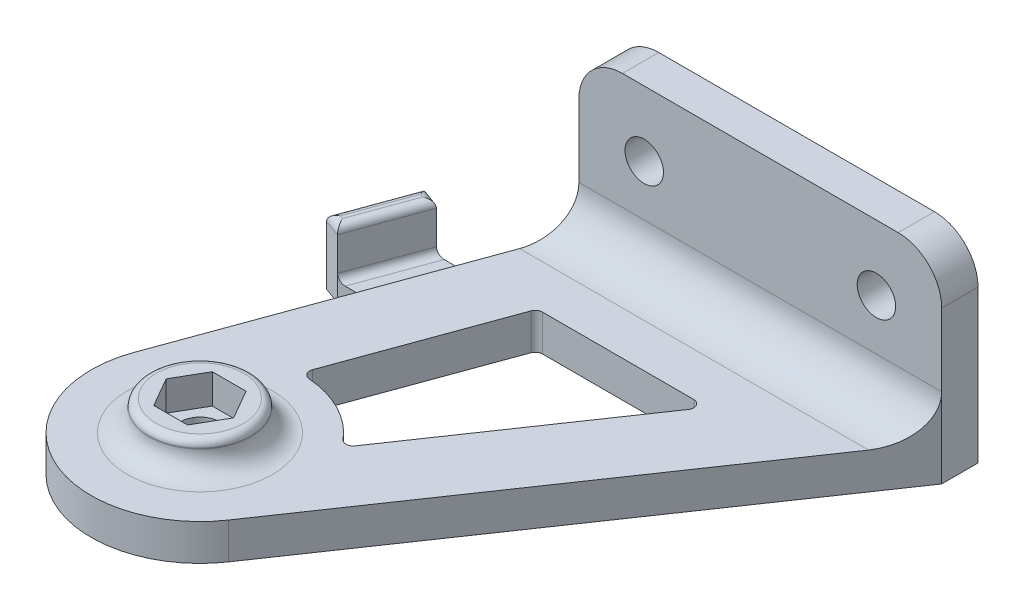
SolidWorks part; units mm, degrees
ref_plane "Front Plane" through (0, 0, 0) normal (0, 0, 1) x (1, 0, 0)
ref_plane "Top Plane" through (0, 0, 0) normal (0, 1, 0) x (1, 0, 0)
ref_plane "Right Plane" through (0, 0, 0) normal (1, 0, 0) x (0, 0, -1)
sketch "Sketch1" plane through (0, 0, 0) normal (0, 0, 1) x (1, 0, 0)
  line L1 (0, 0) -> (-300, 0)
  line L2 (0, 0) -> (0, -20)
  line L3 (0, -20) -> (-300, -20)
  line L4 (-300, 0) -> (-300, -20)
  line L5 (0, 0) -> (-18, 0)
  line L6 (0, 0) -> (0, -20)
  line L7 (0, -20) -> (-18, -20)
  line L8 (-18, 0) -> (-18, -20)
  dimension "D1" = 20
  dimension "D2" = 300
  dimension "D3" = 18
sketch "Sketch2" plane through (0, 0, 0) normal (1, 0, 0) x (0, 0, -1)
  line L1 (0, -20) -> (20, -20)
  line L2 (0, -20) -> (0, -320)
  line L3 (0, -320) -> (20, -320)
  line L4 (20, -20) -> (20, -320)
  line L5 (0, -20) -> (20, -20)
  line L6 (0, -20) -> (0, -38)
  line L7 (0, -38) -> (20, -38)
  line L8 (20, -20) -> (20, -38)
  dimension "D1" = 20
  dimension "D2" = 300
  dimension "D3" = 18
sketch "Sketch3" plane through (0, 0, 0) normal (0, 0, 1) x (1, 0, 0)
  line L1 (-88, -1) -> (-38, -1)
  line L2 (-88, -1) -> (-88, -28)
  line L3 (-88, -28) -> (-38, -28)
  line L4 (-38, -1) -> (-38, -28)
  line L5 (-18, 0) -> (-18, -20) construction
  line L6 (0, 0) -> (-300, 0) construction
  line L7 (0, -20) -> (-300, -20) construction
  dimension "D1" = 20
  dimension "D2" = 1
  dimension "D3" = 50
  dimension "D4" = 8
extrude "Boss-Extrude1" add sketch "Sketch3" along normal blind 5 contours L3 L4 L1 L2
sketch "Sketch5" plane through (0, -28, 0) normal (0, -1, 0) x (1, 0, 0)
  line L0 (-38, 5) -> (-77.8415, 63.4486)
  line L1 (-104.3312, 49.8697) -> (-88, 5)
  line L2 (-88, 5) -> (-88, 0)
  line L3 (-88, 0) -> (-38, 0)
  line L4 (-38, 0) -> (-38, 5)
  line L5 (-88, 5) -> (-88, 0) construction
  line L6 (-88, 5) -> (-38, 5) construction
  arc A0 (-77.8415, 63.4486) -> (-104.3312, 49.8697) centre (-90.2358, 55) ccw
  dimension "D2" = 15
  dimension "D1" = 160
  dimension "D3" = 50
extrude "Boss-Extrude2" add sketch "Sketch5" against normal blind 5
hole_wizard "M5 Clearance Hole1" positions "Sketch6" profile "Sketch7" hole size "M5" standard "ISO" end condition through all
sketch "Sketch6" plane through (0, 0, 5) normal (0, 0, 1) x (1, 0, 0)
  line L0 (-79, -10) -> (-47, -10) construction
  line L2 (-63, -10) -> (-63, -1) construction
  line L3 (-88, -1) -> (-38, -1) construction
  line L5 (0, 0) -> (-300, 0) construction
  point P0 (-79, -10)
  point P2 (-47, -10)
  dimension "D1" = 10
  dimension "D2" = 32
sketch "Sketch7" plane through (-79, -10, 5) normal (1, 0, 0) x (0, -1, 0)
  line L0 (0, 0) -> (0, 5)
  line L1 (0, 5) -> (2.65, 5)
  line L2 (2.65, 5) -> (2.65, 0)
  line L5 (2.65, 0) -> (0, 0)
  line L11 (0, -6.35) -> (0, 107.95) construction
  dimension "Thru Hole Dia." = 5.3
  dimension "Thru Hole Depth" = 5
fillet "Fillet1" radius 6 3 edges at (-88, -1, 2.5) (-38, -1, 2.5) (-63, -23, 5)
hole_wizard "M5 Clearance Hole2" positions "Sketch8" profile "Sketch9" hole size "M5" standard "ISO" end condition through all
sketch "Sketch8" plane through (0, -23, 0) normal (0, 1, 0) x (1, 0, 0)
  point P0 (-90.2358, -55)
sketch "Sketch9" plane through (-90.2358, -23, 55) normal (1, 0, 0) x (0, 0, 1)
  line L0 (0, 0) -> (0, 5)
  line L1 (0, 5) -> (2.65, 5)
  line L2 (2.65, 5) -> (2.65, 0)
  line L5 (2.65, 0) -> (0, 0)
  line L11 (0, -6.35) -> (0, 107.95) construction
  dimension "Thru Hole Dia." = 5.3
  dimension "Thru Hole Depth" = 5
sketch "Sketch10" plane through (0, -23, 0) normal (0, 1, 0) x (1, 0, 0)
  line L0 (-42.0899, -11) -> (-90.1838, -11) construction
  line L1 (-92.5626, -50.97) -> (-94.8893, -55)
  line L2 (-94.8893, -55) -> (-92.5626, -59.03)
  line L3 (-92.5626, -59.03) -> (-87.9091, -59.03)
  line L4 (-87.9091, -59.03) -> (-85.5824, -55)
  line L5 (-85.5824, -55) -> (-87.9091, -50.97)
  line L6 (-87.9091, -50.97) -> (-92.5626, -50.97)
  circle A0 centre (-90.2358, -55) radius 4.03 construction
  dimension "D1" = 8.06
sketch "Sketch11" plane through (0, -23, 0) normal (0, 1, 0) x (1, 0, 0)
  circle A0 centre (-90.2358, -55) radius 7
  dimension "D1" = 14
extrude "Boss-Extrude3" add sketch "Sketch11" along normal blind 4.1
extrude "Cut-Extrude1" cut sketch "Sketch10" along normal through all
fillet "Fillet2" radius 3 1 edges at (-90.2358, -23, 48)
fillet "Fillet3" radius 1 1 edges at (-90.2358, -18.9, 62)
sketch "Sketch12" plane through (0, 0, 0) normal (0, 0, -1) x (-1, 0, 0)
  line L0 (47, -10) -> (63, -10) construction
  line L1 (56, -12.25) -> (70, -12.25)
  line L2 (56, -12.25) -> (56, -7.75)
  line L3 (56, -7.75) -> (70, -7.75)
  line L4 (70, -12.25) -> (70, -7.75)
  line L5 (56, -12.25) -> (70, -7.75) construction
  line L6 (56, -7.75) -> (70, -12.25) construction
  line L7 (63, -10) -> (79, -10) construction
  circle A0 centre (79, -10) radius 2.65 construction
  point P0 (63, -10)
  dimension "D1" = 4.5
  dimension "D2" = 14
extrude "Boss-Extrude4" add sketch "Sketch12" along normal blind 2.5
sketch "Sketch13" plane through (0, -28, 0) normal (0, -1, 0) x (1, 0, 0)
  line L0 (-91.6397, 15) -> (-97.6397, 15)
  line L1 (-104.3312, 49.8697) -> (-88, 5) construction
  line L2 (-97.6397, 15) -> (-101.2794, 25)
  line L3 (-101.2794, 25) -> (-95.2794, 25)
  line L4 (-95.2794, 25) -> (-91.6397, 15)
  line L5 (-88, 0) -> (-38, 0) construction
  dimension "D1" = 6
  dimension "D2" = 10
  dimension "D3" = 15
extrude "Boss-Extrude5" add sketch "Sketch13" against normal offset from surface (2.5 mm away) 2.5 up to face at (-90.2358, -23, 45)
sketch "Sketch14" plane through (-81.3971, 0, -29.6261) normal (-0.9397, 0, -0.342) x (-0.342, 0, 0.9397)
  line L0 (58.1319, -28) -> (58.1319, -18.9)
  line L1 (58.1319, -18.9) -> (47.4901, -18.9)
  line L2 (47.4901, -18.9) -> (47.4901, -28)
  line L3 (47.4901, -28) -> (58.1319, -28)
  line L6 (88.5456, -18.9) -> (76.5456, -18.9) construction
extrude "Boss-Extrude6" add sketch "Sketch14" along normal blind 2.5
fillet "Fillet4" radius 1 6 edges at (-102.454, -18.9, 24.5725) (-101.8088, -18.9, 19.1449) (-98.8143, -18.9, 14.5725) (-99.4596, -18.9, 20) (-93.4596, -25.5, 20) (-99.4596, -25.5, 20)
sketch "Sketch15" plane through (0, -23, 0) normal (0, 1, 0) x (1, 0, 0)
  line L0 (-81.7259, -17) -> (-58.282, -17)
  line L1 (-58.282, -17) -> (-78.739, -47.011)
  line L2 (-90.4618, -41.0018) -> (-81.7259, -17)
  line L3 (-42.0899, -11) -> (-90.1838, -11) construction
  line L4 (-42.0899, -11) -> (-77.8415, -63.4486) construction
  line L5 (-104.3312, -49.8697) -> (-90.1838, -11) construction
  arc A0 (-78.739, -47.011) -> (-90.4618, -41.0018) centre (-90.2358, -55) ccw
  circle A1 centre (-90.2358, -55) radius 10 construction
  dimension "D1" = 6
  dimension "D2" = 10
  dimension "D3" = 10
  dimension "D4" = 4
extrude "Cut-Extrude2" cut sketch "Sketch15" against normal through all
fillet "Fillet5" radius 1 4 edges at (-58.282, -25.5, 17) (-78.739, -25.5, 47.011) (-90.4618, -25.5, 41.0018) (-81.7259, -25.5, 17)
equation "\"D3@Sketch15\"=\"D2@Sketch15\""
